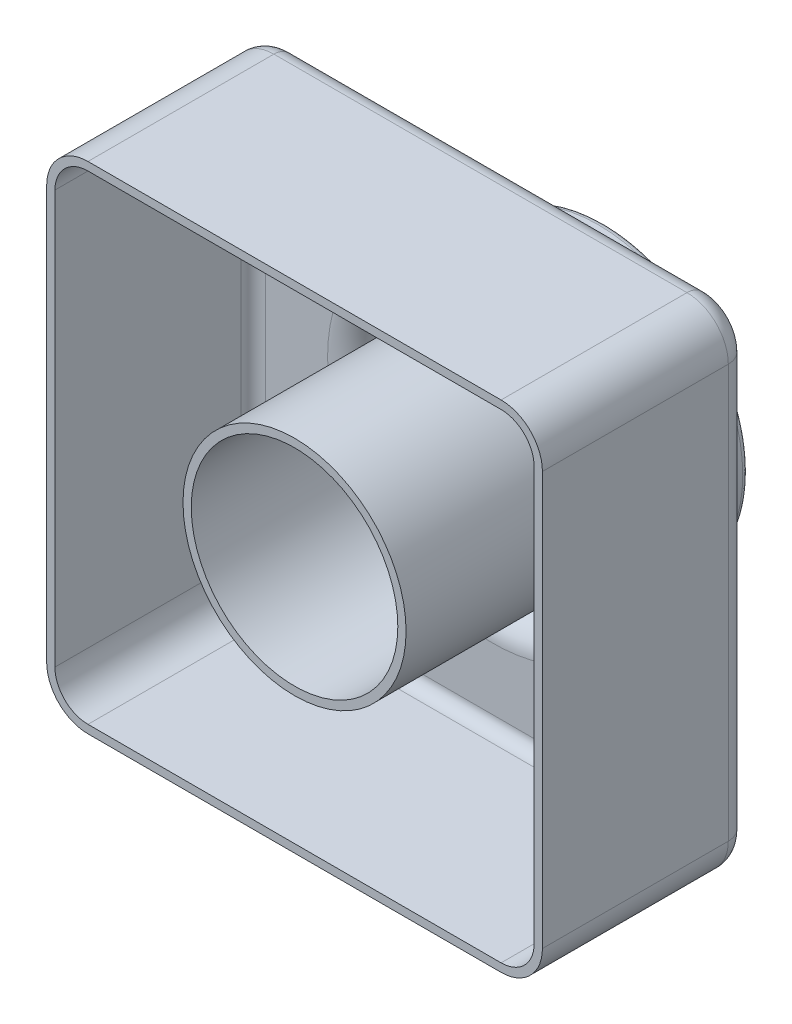
SolidWorks part; units mm, degrees
material "Chrome Stainless Steel"
ref_plane "Front Plane" through (0, 0, 0) normal (0, 0, 1) x (1, 0, 0)
ref_plane "Top Plane" through (0, 0, 0) normal (0, 1, 0) x (1, 0, 0)
ref_plane "Right Plane" through (0, 0, 0) normal (1, 0, 0) x (0, 0, -1)
sketch "Sketch2" plane through (0, 0, 0) normal (0, 0, 1) x (1, 0, 0)
  line L1 (0, 0) -> (120, 0)
  line L2 (0, 0) -> (0, 120)
  line L3 (0, 120) -> (120, 120)
  line L4 (120, 0) -> (120, 120)
  dimension "D1" = 120
  dimension "D2" = 120
extrude "Boss-Extrude2" add sketch "Sketch2" along normal blind 50
sketch "Sketch4" plane through (0, 0, 0) normal (0, 0, -1) x (-1, 0, 0)
  line L0 (-120, 120) -> (0, 120) construction
  line L2 (0, 120) -> (0, 0) construction
  circle A0 centre (-60, 60) radius 35
  dimension "D1" = 70
  dimension "D3" = 60
  dimension "D2" = 60
extrude "Boss-Extrude3" add sketch "Sketch4" along normal blind 25
sketch "Sketch5" plane through (0, 0, -25) normal (0, 0, -1) x (-1, 0, 0)
  circle A0 centre (-60, 60) radius 25
  dimension "D1" = 50
extrude "Cut-Extrude1" cut sketch "Sketch5" against normal through all
fillet "Fillet1" radius 10 4 edges at (0, 0, 25) (120, 0, 25) (120, 120, 25) (0, 120, 25)
fillet "Fillet2" radius 1.5 2 edges at (25, 60, -25) (35, 60, -25)
fillet "Fillet3" radius 5 9 edges at (117.0711, 2.9289, 0) (120, 60, 0) (117.0711, 117.0711, 0) (60, 120, 0) (2.9289, 117.0711, 0) (0, 60, 0) (2.9289, 2.9289, 0) (60, 0, 0) (25, 60, 0)
shell "Shell2" thickness 2
